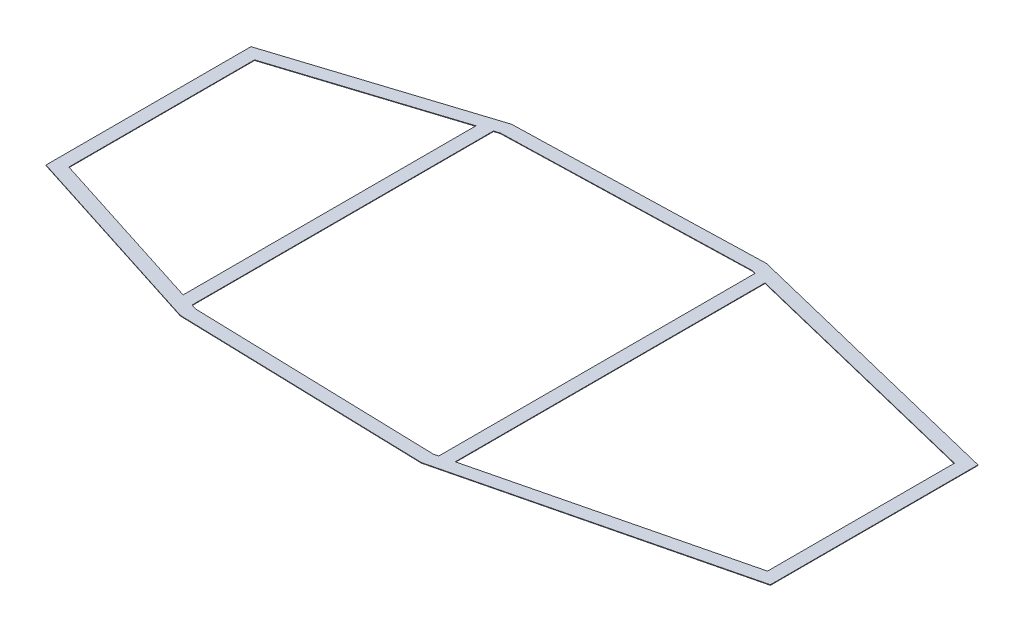
SolidWorks part; units mm, degrees
material "Plain Carbon Steel"
ref_plane "Front Plane" through (0, 0, 0) normal (0, 0, 1) x (1, 0, 0)
ref_plane "Top Plane" through (0, 0, 0) normal (0, 1, 0) x (1, 0, 0)
ref_plane "Right Plane" through (0, 0, 0) normal (1, 0, 0) x (0, 0, -1)
ref_plane "Plane1" through (0, 60.3, 0) normal (0, 1, 0) x (-1, 0, 0)
sketch "Sketch1" plane through (0, 60.3, 0) normal (0, 1, 0) x (-1, 0, 0)
  line L0 (-1080, 317.7) -> (-1080, 0) construction
  line L2 (-1550, 260) -> (-1550, 0) construction
  line L18 (-1580, 292.6204) -> (-2053.8, 176.4663)
  line L19 (-1548.8095, 326.0071) -> (-2082.6095, 195.1438)
  line L20 (-1542.8569, 301.7261) -> (-2076.6569, 170.8628)
  line L21 (-1549.4652, 325.8464) -> (-2078.8, 196.0777)
  line L22 (-1546.7909, 300.7617) -> (-1555, 298.7492)
  line L24 (-1580, -292.6204) -> (-2053.8, -176.4663)
  line L26 (-1549.4652, -325.8464) -> (-2078.8, -196.0777)
  line L56 (0, 0) -> (-3095.2559, 0) construction
  line L62 (-2078.8, 0) -> (-2078.8, 200)
  line L63 (-2078.8, 200) -> (-2078.8, 241.7896)
  line L64 (-2078.8, 241.7896) -> (-1549.6749, 325.8523)
  line L65 (-708, 193.6072) -> (-708, 0)
  line L66 (-1549.6749, 325.8523) -> (-1080.8474, 312.7218)
  line L67 (-1080.8474, 312.7218) -> (-708, 193.6072)
  line L68 (-2078.8, -196.0777) -> (-2078.8, 196.0777)
  line L71 (-708, 193.6072) -> (-708, -193.6072)
  line L72 (-1549.4652, 325.8464) -> (-1080.8474, 312.7218)
  line L73 (-1080.8474, 312.7218) -> (-708, 193.6072)
  line L91 (-1580, 292.6204) -> (-1580, -292.6204)
  line L95 (-2053.8, 0) -> (-2053.8, 200)
  line L96 (-2053.8, 200) -> (-2053.8, 220.4478)
  line L97 (-2053.8, 220.4478) -> (-1548.0497, 300.797)
  line L98 (-1548.0497, 300.797) -> (-1085.0846, 287.8306)
  line L99 (-1085.0846, 287.8306) -> (-733, 175.3493)
  line L100 (-733, 175.3493) -> (-733, 0)
  line L101 (-2053.8, -176.4663) -> (-2053.8, 176.4663)
  line L104 (-1546.7909, 300.7617) -> (-1085.0846, 287.8306)
  line L105 (-1085.0846, 287.8306) -> (-1075, 284.6089)
  line L106 (-733, 175.3493) -> (-733, -175.3493)
  line L113 (-1050, 317.7) -> (-1050, 0)
  line L114 (-1050, 276.6221) -> (-1050, -276.6221)
  line L116 (-1050, -276.6221) -> (-733, -175.3493)
  line L117 (-1085.0846, -287.8306) -> (-1075, -284.6089)
  line L118 (-1050, 276.6221) -> (-733, 175.3493)
  line L119 (-1555, 324.5133) -> (-1555, 0)
  line L120 (-1555, 298.7492) -> (-1555, -298.7492)
  line L121 (-1075, 284.6089) -> (-1075, -284.6089)
  line L122 (-1548.0497, -300.797) -> (-1085.0846, -287.8306)
  line L125 (-1555, -298.7492) -> (-1548.0497, -300.797)
  line L126 (-1080.8474, -312.7218) -> (-708, -193.6072)
  line L127 (-1549.4652, -325.8464) -> (-1080.8474, -312.7218)
  point P1 (-1080, 317.7)
  point P2 (-1550, 330.8633)
  point P3 (-2084.7554, 199.7658)
  point P4 (-2083.8, 0)
  point P5 (-2083.8, -200)
  point P6 (-1550, -330.8633)
  point P7 (-1080, -317.7)
  point P10 (-1080, 0)
  point P11 (-1550, 0)
  point P14 (-723, 182.6524)
  point P15 (-1086.0864, 298.6486)
  point P17 (-723, -182.6524)
  point P18 (-1086.0864, -298.6486)
  point P19 (-1080.5599, -297.7078)
  point P20 (-1550.5599, -310.8712)
  point P21 (-1545.2379, -311.4385)
  point P22 (-2063.8, -184.3108)
  point P24 (-2063.8, 184.3108)
  point P25 (-1545.2379, 311.4385)
  point P26 (-1080.5599, 297.7078)
  point P27 (-1550.5599, 310.8712)
  point P28 (-1100, -317.7)
  point P29 (-1100, 0)
  point P30 (-1100, 317.7)
  point P31 (-1530, 0)
  point P32 (-1530, 330.8633)
  point P33 (-1530, -330.8633)
  point P53 (-1075, 0)
  point P63 (-1580, 0)
  dimension "D3" = 5
  dimension "D4" = 30
  dimension "D5" = 30
  dimension "D1" = 5
  dimension "D2" = 30
  dimension "D6" = 5
  dimension "D7" = 5
  dimension "D8" = 30
extrude "Boss-Extrude1" add sketch "Sketch1" along normal blind 1
